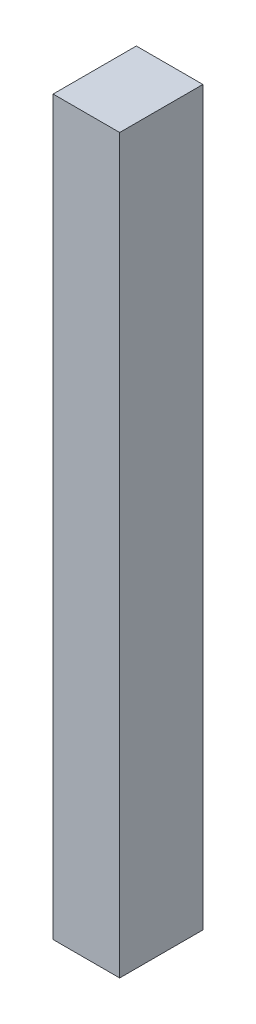
SolidWorks part; units mm, degrees
ref_plane "Plan de face" through (0, 0, 0) normal (0, 0, 1) x (1, 0, 0)
ref_plane "Plan de dessus" through (0, 0, 0) normal (0, 1, 0) x (1, 0, 0)
ref_plane "Plan de droite" through (0, 0, 0) normal (1, 0, 0) x (0, 0, -1)
sketch "Esquisse1" plane through (0, 0, 0) normal (0, 0, 1) x (1, 0, 0)
  line L1 (-40, 440) -> (40, 440)
  line L2 (-40, 440) -> (-40, -440)
  line L3 (-40, -440) -> (40, -440)
  line L4 (40, 440) -> (40, -440)
  line L5 (-40, 440) -> (40, -440) construction
  line L6 (-40, -440) -> (40, 440) construction
  point P0 (0, 0)
  dimension "D1" = 880
  dimension "D2" = 80
extrude "Boss.-Extru.1" add sketch "Esquisse1" along normal blind 100
